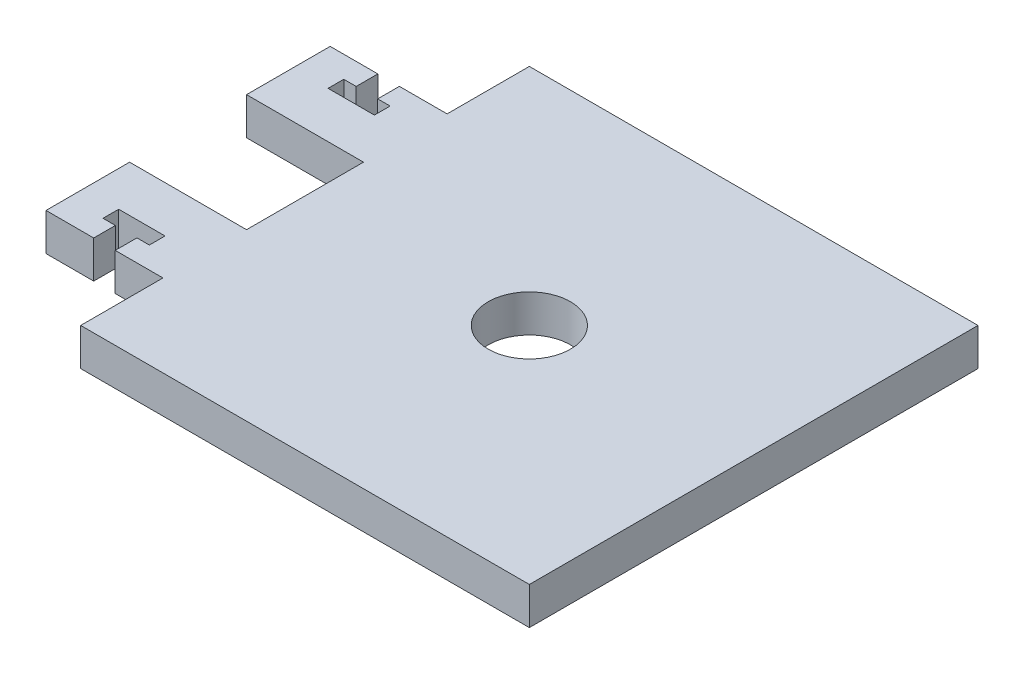
SolidWorks part; units mm, degrees
ref_plane "Front Plane" through (0, 0, 0) normal (0, 0, 1) x (1, 0, 0)
ref_plane "Top Plane" through (0, 0, 0) normal (0, 1, 0) x (1, 0, 0)
ref_plane "Right Plane" through (0, 0, 0) normal (1, 0, 0) x (0, 0, -1)
sketch "Sketch1" plane through (0, 0, 0) normal (0, 1, 0) x (1, 0, 0)
  line L0 (0, 0) -> (38.1, 0) construction
  line L1 (-38.1, -38.1) -> (38.1, -38.1)
  line L2 (-38.1, -38.1) -> (-38.1, -24.13)
  line L3 (-38.1, 38.1) -> (38.1, 38.1)
  line L4 (38.1, -38.1) -> (38.1, 38.1)
  line L5 (-38.1, -38.1) -> (38.1, 38.1) construction
  line L6 (-38.1, 38.1) -> (38.1, -38.1) construction
  line L7 (0, 0) -> (0, -18.5806) construction
  line L8 (-38.1, -24.13) -> (-46.2026, -24.13)
  line L9 (-57.9628, -24.13) -> (-57.9628, -9.9314)
  line L10 (-57.9628, -9.9314) -> (-38.1, -9.9314)
  line L12 (-38.1, 24.13) -> (-46.2026, 24.13)
  line L13 (-57.9628, 9.9314) -> (-38.1, 9.9314)
  line L14 (-57.9628, 24.13) -> (-57.9628, 9.9314)
  line L15 (-38.1, 24.13) -> (-38.1, 38.1)
  line L16 (-38.1, -9.9314) -> (-38.1, 9.9314)
  line L17 (-48.0314, -24.13) -> (-48.0314, -17.78) construction
  line L19 (-46.2026, -24.13) -> (-46.2026, -20.447)
  line L20 (-46.2026, -20.447) -> (-44.0944, -20.447)
  line L21 (-44.0944, -20.447) -> (-44.0944, -17.78)
  line L22 (-44.0944, -17.78) -> (-51.9684, -17.78)
  line L23 (-49.8602, -24.13) -> (-49.8602, -20.447)
  line L24 (-49.8602, -20.447) -> (-51.9684, -20.447)
  line L25 (-51.9684, -20.447) -> (-51.9684, -17.78)
  line L26 (-49.8602, 20.447) -> (-51.9684, 20.447)
  line L27 (-49.8602, 24.13) -> (-49.8602, 20.447)
  line L28 (-46.2026, 24.13) -> (-46.2026, 20.447)
  line L29 (-46.2026, 20.447) -> (-44.0944, 20.447)
  line L30 (-44.0944, 20.447) -> (-44.0944, 17.78)
  line L31 (-44.0944, 17.78) -> (-51.9684, 17.78)
  line L32 (-51.9684, 20.447) -> (-51.9684, 17.78)
  line L33 (-49.8602, -24.13) -> (-57.9628, -24.13)
  line L34 (-49.8602, 24.13) -> (-57.9628, 24.13)
  circle A0 centre (0, 0) radius 6.985
  point P0 (0, 0)
  point P11 (0, -18.5806)
  point P25 (0, 0)
  point P35 (0, 0)
  dimension "D2" = 13.97
  dimension "D1" = 45
  dimension "D3" = 76.2
  dimension "D4" = 13.97
  dimension "D5" = 14.1986
  dimension "D6" = 19.8628
  dimension "D7" = 7.874
  dimension "D8" = 2.667
  dimension "D9" = 6.35
  dimension "D10" = 3.6576
extrude "Boss-Extrude1" add sketch "Sketch1" against normal blind 6.35
